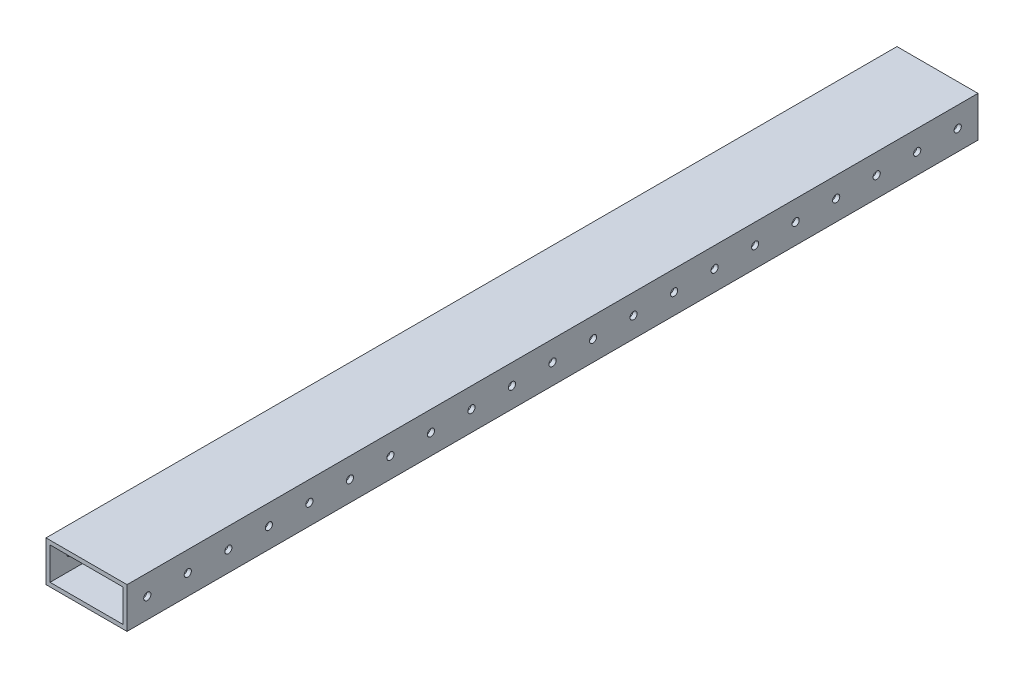
SolidWorks part; units mm, degrees
ref_plane "Front Plane" through (0, 0, 0) normal (0, 0, 1) x (1, 0, 0)
ref_plane "Top Plane" through (0, 0, 0) normal (0, 1, 0) x (1, 0, 0)
ref_plane "Right Plane" through (0, 0, 0) normal (1, 0, 0) x (0, 0, -1)
sketch "Sketch1" plane through (0, 0, 0) normal (0, 0, 1) x (1, 0, 0)
  line L1 (-25.4, -12.7) -> (25.4, -12.7)
  line L2 (-25.4, -12.7) -> (-25.4, 12.7)
  line L3 (-25.4, 12.7) -> (25.4, 12.7)
  line L4 (25.4, -12.7) -> (25.4, 12.7)
  line L5 (-25.4, -12.7) -> (25.4, 12.7) construction
  line L6 (-25.4, 12.7) -> (25.4, -12.7) construction
  line L7 (-22.86, -10.16) -> (22.86, -10.16)
  line L8 (-22.86, -10.16) -> (-22.86, 10.16)
  line L9 (-22.86, 10.16) -> (22.86, 10.16)
  line L10 (22.86, -10.16) -> (22.86, 10.16)
  line L11 (-22.86, -10.16) -> (22.86, 10.16) construction
  line L12 (-22.86, 10.16) -> (22.86, -10.16) construction
  point P0 (0, 0)
  point P6 (0, 0)
  dimension "D1" = 50.8
  dimension "D2" = 25.4
  dimension "D3" = 2.54
  dimension "D4" = 2.54
extrude "Boss-Extrude1" add sketch "Sketch1" against normal blind 533.4
hole_wizard "#8 Clearance Hole1" positions "Sketch2" profile "Sketch3" hole size "#8" standard "ANSI Inch" end condition through all
sketch "Sketch2" plane through (25.4, 0, 0) normal (1, 0, 0) x (0, 0, -1)
  line L0 (533.4, -12.7) -> (0, -12.7) construction
  line L1 (533.4, -12.7) -> (533.4, 12.7) construction
  point P0 (12.7, 0)
  point P16 (38.1, 0)
  point P17 (63.5, 0)
  point P18 (88.9, 0)
  point P19 (114.3, 0)
  point P20 (139.7, 0)
  point P21 (165.1, 0)
  point P22 (190.5, 0)
  point P23 (215.9, 0)
  point P24 (241.3, 0)
  point P25 (266.7, 0)
  point P26 (292.1, 0)
  point P27 (317.5, 0)
  point P28 (342.9, 0)
  point P29 (368.3, 0)
  point P30 (393.7, 0)
  point P31 (419.1, 0)
  point P32 (444.5, 0)
  point P33 (469.9, 0)
  point P34 (495.3, 0)
  point P35 (520.7, 0)
  dimension "D1" = 12.7
  dimension "D2" = 12.7
  dimension "D3" = 21
sketch "Sketch3" plane through (25.4, 0, -12.7) normal (0, 1, 0) x (0, 0, -1)
  line L0 (0, 0) -> (0, 50.8)
  line L1 (0, 50.8) -> (2.2479, 50.8)
  line L2 (2.2479, 50.8) -> (2.2479, 0)
  line L5 (2.2479, 0) -> (0, 0)
  line L11 (0, -6.35) -> (0, 107.95) construction
  dimension "Thru Hole Dia." = 4.4958
  dimension "Thru Hole Depth" = 50.8
